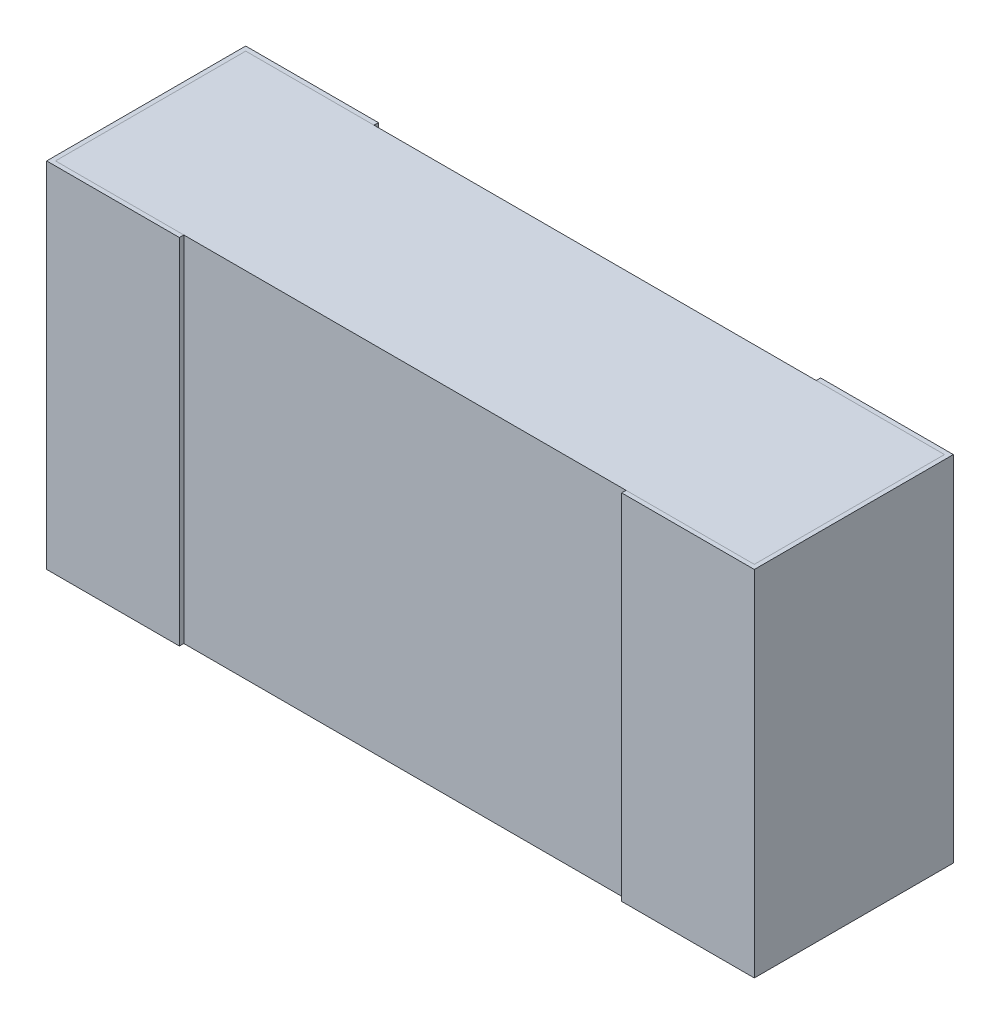
SolidWorks part; units mm, degrees
ref_plane "Front Plane" through (0, 0, 0) normal (0, 0, 1) x (1, 0, 0)
ref_plane "Top Plane" through (0, 0, 0) normal (0, 1, 0) x (1, 0, 0)
ref_plane "Right Plane" through (0, 0, 0) normal (1, 0, 0) x (0, 0, -1)
sketch "Sketch4" plane through (0, 0, 0) normal (0, 1, 0) x (-1, 0, 0)
  line L0 (0, 0.1169) -> (0, -0.0721) construction
  line L1 (-0.8, -0.2366) -> (0.3669, -0.2366) construction
  line L2 (-0.8, -0.0116) -> (-0.8, -0.4616)
  line L3 (-0.8, -0.4616) -> (-0.5, -0.4616)
  line L4 (-0.5, -0.0116) -> (-0.5, -0.0216)
  line L5 (-0.5, -0.0216) -> (-0.79, -0.0216)
  line L6 (-0.79, -0.0216) -> (-0.79, -0.4516)
  line L7 (-0.79, -0.4516) -> (-0.5, -0.4516)
  line L8 (-0.5, -0.4516) -> (-0.5, -0.4616)
  line L9 (-0.5, -0.0116) -> (-0.8, -0.0116)
  line L10 (0.5, -0.0116) -> (0.8, -0.0116)
  line L11 (0.5, -0.4516) -> (0.5, -0.4616)
  line L12 (0.79, -0.4516) -> (0.5, -0.4516)
  line L13 (0.79, -0.0216) -> (0.79, -0.4516)
  line L14 (0.5, -0.0216) -> (0.79, -0.0216)
  line L15 (0.5, -0.0116) -> (0.5, -0.0216)
  line L16 (0.8, -0.4616) -> (0.5, -0.4616)
  line L17 (0.8, -0.0116) -> (0.8, -0.4616)
  dimension "LENGTH" = 0.8
  dimension "HEIGHT" = 0.45
  dimension "END CAP TOP LENGTH" = 0.3
  dimension "END CAP BOTTOM LENGTH" = 0.3
  dimension "D5" = 0.01
  dimension "D6" = 0.01
extrude "Boss-Extrude2" add sketch "Sketch4" along normal mid plane 0.8
sketch "Sketch5" plane through (0, 0, 0) normal (0, 1, 0) x (0, 0, -1)
  line L1 (0.0216, -0.79) -> (0.4516, -0.79)
  line L2 (0.0216, -0.79) -> (0.0216, 0.79)
  line L3 (0.0216, 0.79) -> (0.4516, 0.79)
  line L4 (0.4516, -0.79) -> (0.4516, 0.79)
extrude "Boss-Extrude3" add sketch "Sketch5" along normal up to surface and the other way up to surface separate body
